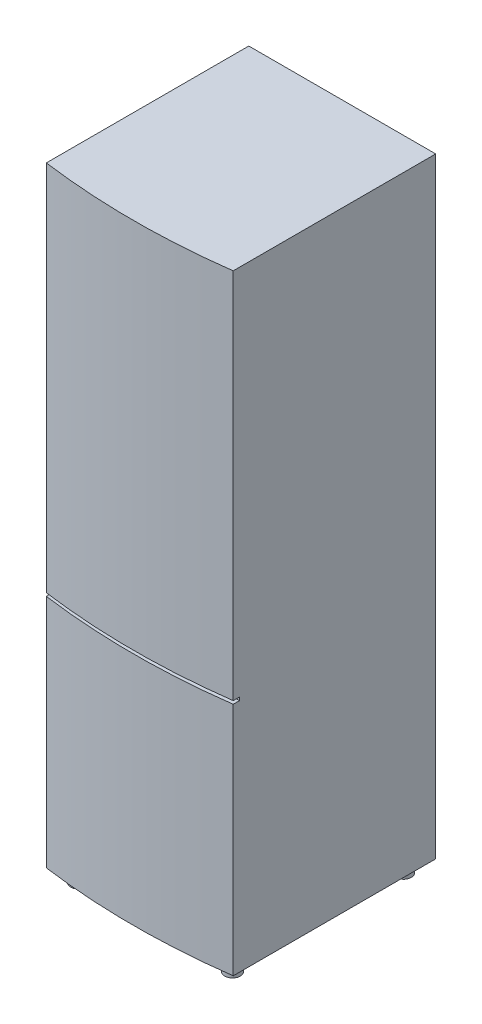
SolidWorks part; units mm, degrees
ref_plane "Front Plane" through (0, 0, 0) normal (0, 0, 1) x (1, 0, 0)
ref_plane "Top Plane" through (0, 0, 0) normal (0, 1, 0) x (1, 0, 0)
ref_plane "Right Plane" through (0, 0, 0) normal (1, 0, 0) x (0, 0, -1)
sketch "Sketch1" plane through (0, 0, 0) normal (0, 1, 0) x (1, 0, 0)
  line L2 (300, -325) -> (300, 325)
  line L3 (300, 325) -> (-300, 325)
  line L4 (-300, -325) -> (-300, 325)
  line L5 (300, -325) -> (-300, 325) construction
  line L6 (300, 325) -> (-300, -325) construction
  arc A0 (-300, -325) -> (300, -325) centre (0, 1894.495) ccw
  point P0 (0, 0)
  dimension "D1" = 600
  dimension "D2" = 650
extrude "Boss-Extrude1" add sketch "Sketch1" along normal blind 1960
sketch "Sketch2" plane through (0, 0, 0) normal (0, -1, 0) x (1, 0, 0)
  line L5 (247.4212, -274.4131) -> (-247.4212, 274.4131) construction
  line L6 (247.4212, 274.4131) -> (-247.4212, -274.4131) construction
  circle A0 centre (-247.4212, 274.4131) radius 25
  circle A1 centre (247.4212, 274.4131) radius 25
  circle A2 centre (247.4212, -274.4131) radius 25
  circle A3 centre (-247.4212, -274.4131) radius 25
  point P0 (0, 0)
  dimension "D1" = 50
extrude "Boss-Extrude2" add sketch "Sketch2" along normal blind 40
ref_plane "Plane1" through (0, 0, 475) normal (0, 0, -1) x (-1, 0, 0)
sketch "Sketch3" plane through (0, 0, 475) normal (0, 0, -1) x (-1, 0, 0)
  line L0 (-300, 1960) -> (300, 1960) construction
  line L1 (507.0242, 755) -> (-507.0242, 755)
  line L2 (507.0242, 755) -> (507.0242, 765)
  line L3 (507.0242, 765) -> (-507.0242, 765)
  line L4 (-507.0242, 755) -> (-507.0242, 765)
  line L5 (507.0242, 755) -> (-507.0242, 765) construction
  line L6 (507.0242, 765) -> (-507.0242, 755) construction
  point P0 (0, 760)
  dimension "D1" = 10
  dimension "D2" = 1200
extrude "Cut-Extrude1" cut sketch "Sketch3" along normal blind 170
